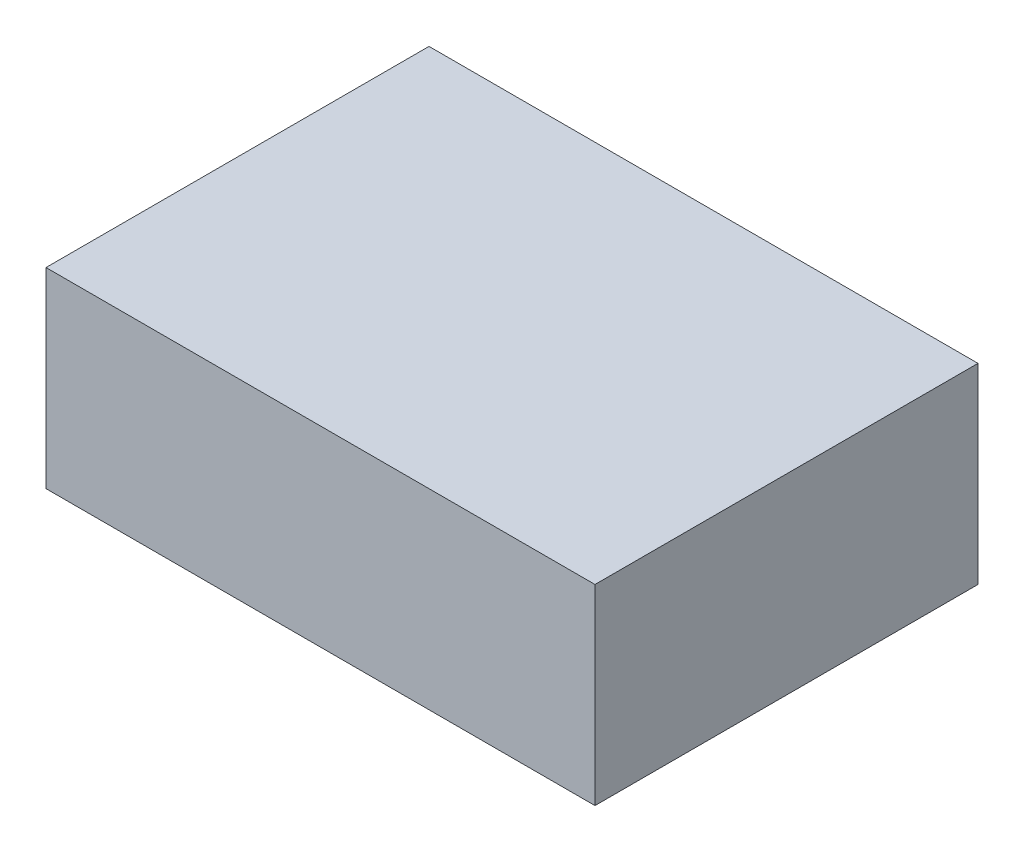
SolidWorks part; units mm, degrees
ref_plane "Front Plane" through (0, 0, 0) normal (0, 0, 1) x (1, 0, 0)
ref_plane "Top Plane" through (0, 0, 0) normal (0, 1, 0) x (1, 0, 0)
ref_plane "Right Plane" through (0, 0, 0) normal (1, 0, 0) x (0, 0, -1)
sketch "Sketch1" plane through (0, 0, 0) normal (0, 1, 0) x (1, 0, 0)
  line L1 (0, 0) -> (43, 0)
  line L2 (0, 0) -> (0, 30)
  line L3 (0, 30) -> (43, 30)
  line L4 (43, 0) -> (43, 30)
  dimension "D1" = 43
  dimension "D2" = 30
extrude "Boss-Extrude1" add sketch "Sketch1" along normal blind 15
